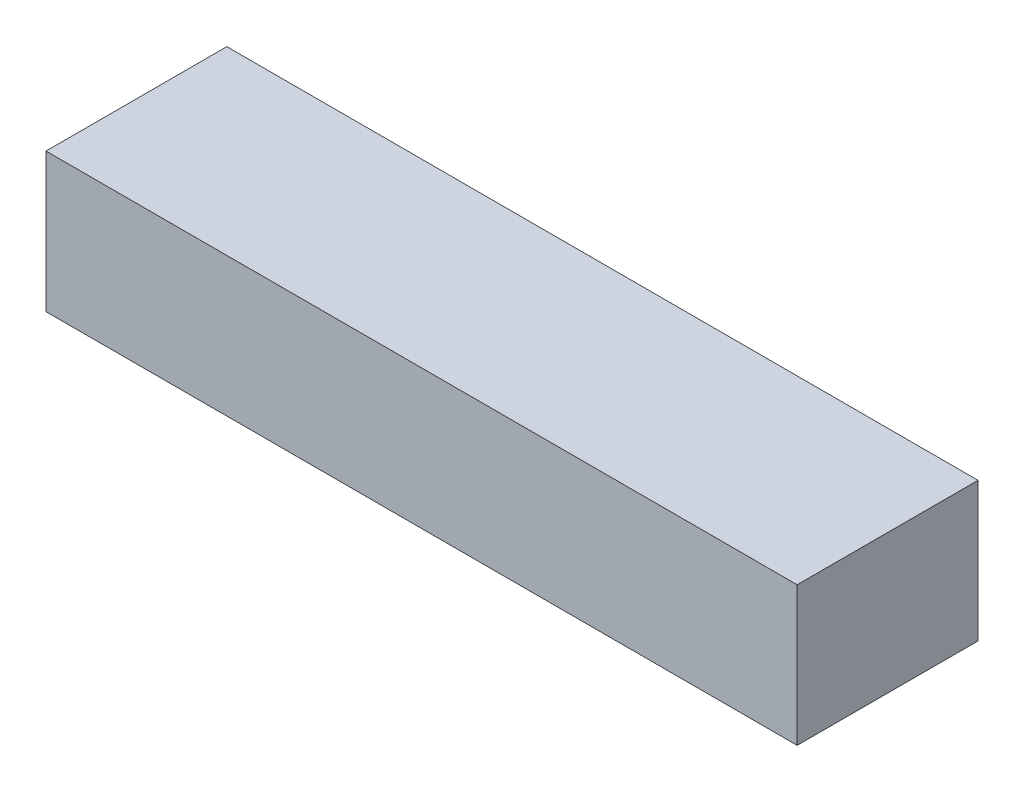
SolidWorks part; units mm, degrees
ref_plane "Front Plane" through (0, 0, 0) normal (0, 0, 1) x (1, 0, 0)
ref_plane "Top Plane" through (0, 0, 0) normal (0, 1, 0) x (1, 0, 0)
ref_plane "Right Plane" through (0, 0, 0) normal (1, 0, 0) x (0, 0, -1)
sketch "Sketch1" plane through (0, 0, 0) normal (0, 1, 0) x (1, 0, 0)
  line L1 (-150.0101, 20.4074) -> (119.9899, 20.4074)
  line L2 (-150.0101, 20.4074) -> (-150.0101, -44.5926)
  line L3 (-150.0101, -44.5926) -> (119.9899, -44.5926)
  line L4 (119.9899, 20.4074) -> (119.9899, -44.5926)
  dimension "D1" = 270
  dimension "D2" = 65
extrude "Boss-Extrude1" add sketch "Sketch1" along normal blind 50
sketch "Sketch2" plane through (0, 0, 0) normal (0, 1, 0) x (1, 0, 0)
  line L0 (-150.0101, 20.4074) -> (-150.0101, -44.5926) construction
  line L2 (-150.0101, -44.5926) -> (119.9899, -44.5926) construction
  circle A0 centre (-100.0101, -12.0926) radius 25
  dimension "D1" = 50
  dimension "D2" = 50
  dimension "D3" = 32.5
sketch "Sketch3" plane through (0, 0, 0) normal (0, 1, 0) x (1, 0, 0)
  line L0 (119.9899, -44.5926) -> (119.9899, 20.4074) construction
  line L1 (-150.0101, -44.5926) -> (119.9899, -44.5926) construction
  circle A0 centre (69.9899, -12.0926) radius 25
  dimension "D1" = 50
  dimension "D2" = 50
  dimension "D3" = 32.5
